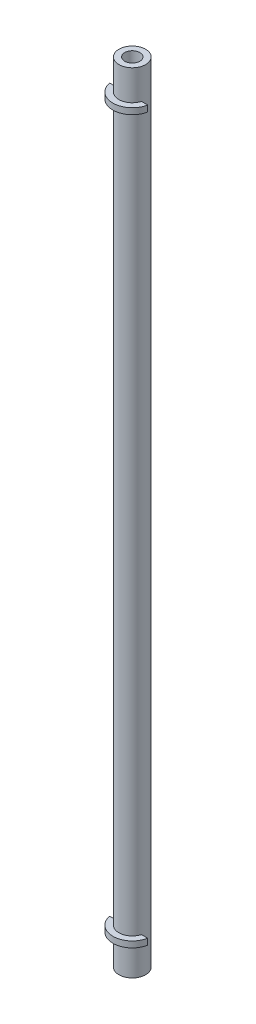
SolidWorks part; units mm, degrees
ref_plane "Front Plane" through (0, 0, 0) normal (0, 0, 1) x (1, 0, 0)
ref_plane "Top Plane" through (0, 0, 0) normal (0, 1, 0) x (1, 0, 0)
ref_plane "Right Plane" through (0, 0, 0) normal (1, 0, 0) x (0, 0, -1)
sketch "Sketch1" plane through (0, 0, 0) normal (0, 1, 0) x (1, 0, 0)
  circle A0 centre (0, 0) radius 2.794
  circle A1 centre (0, 0) radius 1.5875
  dimension "D1" = 5.588
  dimension "D2" = 3.175
extrude "Boss-Extrude1" add sketch "Sketch1" along normal blind 165.1
ref_plane "Plane1" through (0, 6.35, 0) normal (0, -1, 0) x (-1, 0, 0)
sketch "Sketch2" plane through (0, 6.35, 0) normal (0, -1, 0) x (-1, 0, 0)
  line L0 (-3.9919, -0.762) -> (-2.6881, -0.762)
  line L1 (2.6881, -0.762) -> (3.9919, -0.762)
  line L2 (-2.6881, -0.762) -> (2.6881, -0.762) construction
  arc A0 (-3.9919, -0.762) -> (3.9919, -0.762) centre (0, 0) ccw
  circle A1 centre (0, 0) radius 2.794 construction
  circle A2 centre (0, 0) radius 2.794 construction
  arc A4 (-2.6881, -0.762) -> (2.6881, -0.762) centre (0, 0) ccw
  point P1 (0, 0)
  point P9 (0, -2.794)
  dimension "D1" = 1.27
  dimension "D3" = 5.588
  dimension "D2" = 0.762
extrude "Boss-Extrude2" add sketch "Sketch2" against normal blind 1.27
ref_plane "Plane2" through (0, 82.55, 0) normal (0, -1, 0) x (-1, 0, 0)
mirror "Mirror1" about plane through (0, 82.55, 0) normal (0, -1, 0) of "Boss-Extrude2"
